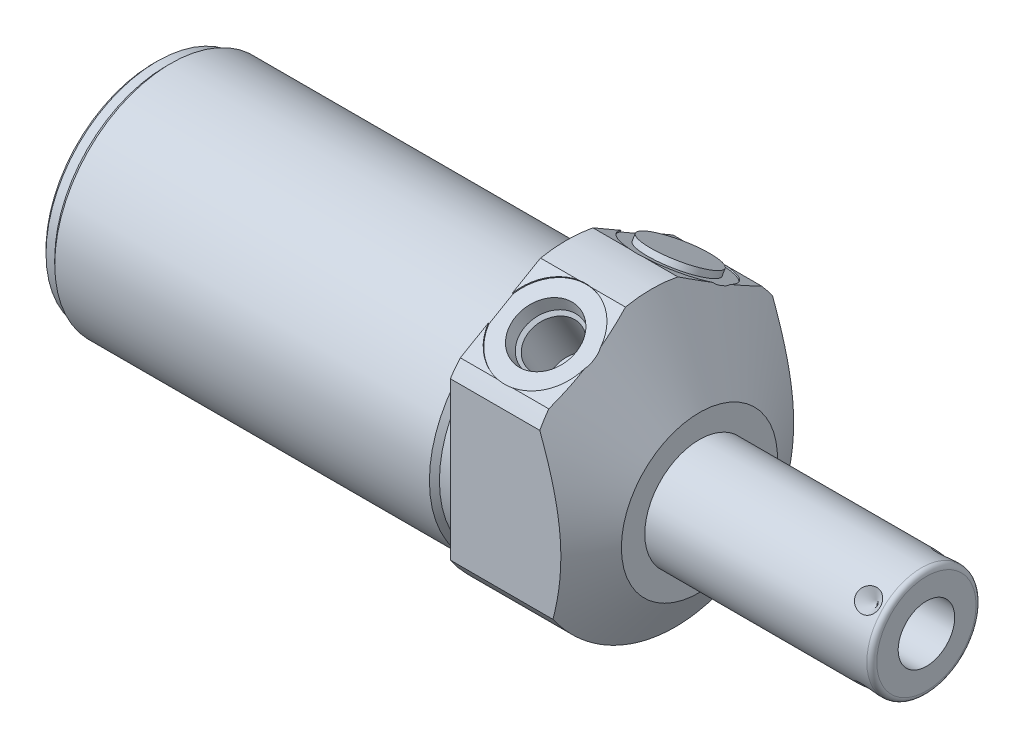
SolidWorks part; units mm, degrees
material "Alloy Steel"
ref_plane "Front Plane" through (0, 0, 0) normal (0, 0, 1) x (1, 0, 0)
ref_plane "Top Plane" through (0, 0, 0) normal (0, 1, 0) x (1, 0, 0)
ref_plane "Right Plane" through (0, 0, 0) normal (1, 0, 0) x (0, 0, -1)
ref_plane "Plane1" through (0, 0, 0) normal (1, 0, 0) x (0, 0, -1)
sketch "Sketch1" plane through (0, 0, 0) normal (1, 0, 0) x (0, 0, -1)
  circle A0 centre (0, 0) radius 28.575
  dimension "D1" = 57.15
extrude "Extrude1" add sketch "Sketch1" along normal blind 27.0002 and the other way blind 84.1248
ref_plane "Plane2" through (0, 0, 0) normal (1, 0, 0) x (0, 0, -1)
sketch "Sketch2" plane through (0, 0, 0) normal (1, 0, 0) x (0, 0, -1)
  line L0 (-25.9842, -4.191) -> (25.9842, -4.191) construction
  circle A0 centre (0, -4.191) radius 23.622
  circle A2 centre (0, 0) radius 28.575
  circle A3 centre (0, 0) radius 28.575
  dimension "D2" = 47.244
  dimension "D1" = 4.191
  dimension "D3" = 0
extrude "Cut-Extrude1" cut sketch "Sketch2" against normal up to next
ref_plane "Plane4" through (0, 0, 0) normal (-1, 0, 0) x (0, 0, 1)
sketch "Sketch4" plane through (0, 0, 0) normal (-1, 0, 0) x (0, 0, 1)
  line L0 (23.6855, -25.6662) -> (23.6855, 17.4761)
  line L1 (23.6855, 17.4761) -> (0, 31.1509)
  line L2 (-23.6855, -25.6662) -> (-23.6855, 17.4761)
  line L3 (-23.6855, 17.4761) -> (0, 31.1509)
  line L4 (0, -31.5613) -> (0, 34.1372) construction
  arc A2 (23.6855, -25.6662) -> (-23.6855, -25.6662) centre (0, 0) ccw
  dimension "D4" = 69.85
  dimension "D1" = 47.371
  dimension "D2" = 30.607
  dimension "D3" = 120
extrude "Cut-Extrude3" cut sketch "Sketch4" against normal up to next
ref_plane "Plane6" through (0, 0, 0) normal (0, 0, 1) x (1, 0, 0)
sketch "Sketch6" plane through (0, 0, 0) normal (0, 0, 1) x (1, 0, 0)
  line L0 (0.7504, 57.15) -> (27.0002, 11.684)
  line L1 (-0.5621, -4.191) -> (28.3127, -4.191) construction
  line L2 (-84.1248, -4.191) -> (0, -4.191) construction
  line L3 (27.0002, 11.684) -> (27.0002, 57.15)
  line L4 (27.0002, 57.15) -> (0.7504, 57.15)
  line L5 (27.0002, 15.9852) -> (27.0002, -15.9852) construction
  dimension "D1" = 60
  dimension "D2" = 31.75
  dimension "D3" = 122.682
revolve "Cut-Revolve2" cut sketch "Sketch6" angle 360 about L1
ref_plane "Plane7" through (9.0932, 23.1369, 13.3727) normal (1, 0, 0) x (0, 0.5, -0.866)
sketch "S2D0002" plane through (9.0932, 23.1369, 13.3727) normal (1, 0, 0) x (0, 0.5, -0.866)
  line L0 (0, 0) -> (6.1849, 0)
  line L1 (6.1849, 0) -> (5.6423, -2.5527)
  line L2 (5.6423, -2.5527) -> (4.9784, -3.2166)
  line L3 (4.9784, -3.2166) -> (4.9784, -13.462)
  line L4 (4.9784, -13.462) -> (0, -13.462)
  line L5 (0, -13.462) -> (0, 0)
  line L6 (0, -14.1351) -> (0, 0.6731) construction
  dimension "D1" = 13.462
revolve "Cut-Revolve3" cut sketch "S2D0002" angle 360 about L6
ref_plane "Plane8" through (9.0932, 23.1369, -13.3727) normal (1, 0, 0) x (0, -0.5, -0.866)
sketch "Sketch8" plane through (9.0932, 23.1369, -13.3727) normal (1, 0, 0) x (0, -0.5, -0.866)
  line L0 (0, 0) -> (6.1849, 0)
  line L1 (6.1849, 0) -> (5.6423, -2.5527)
  line L2 (5.6423, -2.5527) -> (4.9784, -3.2166)
  line L3 (4.9784, -3.2166) -> (4.9784, -13.462)
  line L4 (4.9784, -13.462) -> (0, -13.462)
  line L5 (0, -13.462) -> (0, 0)
  line L6 (0, -14.1351) -> (0, 0.6731) construction
  dimension "D1" = 13.462
revolve "Cut-Revolve4" cut sketch "Sketch8" angle 360 about L6
ref_plane "Plane10" through (0, 0, 0) normal (0, 0, 1) x (1, 0, 0)
sketch "Sketch18" plane through (0, 23.3632, 13.4887) normal (0, 0.866, 0.5) x (1, 0, 0)
  circle A0 centre (9.0932, -0.0127) radius 9.525
  dimension "D1" = 19.05
extrude "Cut-Extrude4" cut sketch "Sketch18" against normal blind 0.254
sketch "Sketch19" plane through (0, 23.3632, -13.4887) normal (0, 0.866, -0.5) x (1, 0, 0)
  circle A0 centre (9.0932, 0.0127) radius 9.525
  circle A1 centre (9.0932, 0.0127) radius 6.1849 construction
  dimension "D1" = 19.05
extrude "Cut-Extrude5" cut sketch "Sketch19" against normal blind 0.254
sketch "Sketch10" plane through (0, 0, 0) normal (0, 0, 1) x (1, 0, 0)
  line L0 (0, 19.431) -> (0, 18.415)
  line L1 (0, 18.415) -> (-3.302, 18.415)
  line L2 (-3.302, 18.415) -> (-4.318, 19.431)
  line L3 (-4.5339, -4.191) -> (0.2159, -4.191) construction
  line L4 (0, 19.431) -> (-4.318, 19.431)
  line L5 (-84.1248, -4.191) -> (0, -4.191) construction
  line L6 (0, 19.431) -> (-84.1248, 19.431) construction
  line L7 (0, 21.9392) -> (0, 18.6529) construction
  dimension "D1" = 45.212
  dimension "D2" = 45
  dimension "D3" = 3.302
revolve "Cut-Revolve6" cut sketch "Sketch10" angle 360 about L3
ref_plane "Plane12" through (0, 0, 0) normal (0, 0, 1) x (1, 0, 0)
sketch "Sketch12" plane through (0, 0, 0) normal (0, 0, 1) x (1, 0, 0)
  line L0 (-84.1248, 19.431) -> (-84.1248, 18.415)
  line L1 (-84.1248, 18.415) -> (-81.5848, 18.415)
  line L2 (-81.5848, 18.415) -> (-80.5688, 19.431)
  line L3 (-84.3026, -4.191) -> (-80.391, -4.191) construction
  line L4 (-84.1248, 19.431) -> (-80.5688, 19.431)
  line L5 (-84.1248, -4.191) -> (-4.318, -4.191) construction
  line L6 (-4.318, 19.431) -> (-84.1248, 19.431) construction
  line L7 (-84.1248, 19.431) -> (-84.1248, -27.813) construction
  dimension "D1" = 45.212
  dimension "D2" = 45
  dimension "D3" = 2.54
revolve "Cut-Revolve8" cut sketch "Sketch12" angle 360 about L3
chamfer "Chamfer1" distance 0.762 angle 45 1 edges at (-84.1248, -4.191, 22.606)
ref_plane "Plane13" through (0, 0, 0) normal (0, 0, 1) x (0, -1, 0)
sketch "Sketch13" plane through (0, 0, 0) normal (0, 0, 1) x (0, -1, 0)
  line L0 (4.191, 27.0002) -> (4.191, 73.2028)
  line L1 (4.191, 73.2028) -> (14.2875, 73.2028)
  line L2 (15.3035, 72.1868) -> (15.3035, 27.0002)
  line L3 (15.3035, 27.0002) -> (4.191, 27.0002)
  line L4 (4.191, 25.1066) -> (4.191, 66.7652) construction
  line L5 (4.191, -80.5688) -> (4.191, -4.318) construction
  line L6 (20.066, 27.0002) -> (-11.684, 27.0002) construction
  line L7 (-18.415, 0) -> (26.797, 0) construction
  arc A0 (15.3035, 72.1868) -> (14.2875, 73.2028) centre (14.2875, 72.1868) ccw
  dimension "D3" = 1.016
  dimension "D1" = 22.225
  dimension "D2" = 73.2028
revolve "Revolve1" add sketch "Sketch13" angle 360 about L4
ref_plane "Plane14" through (64.8716, -9.9441, 0) normal (0, 0, 1) x (0, -1, 0)
sketch "S2D0001" plane through (64.8716, -9.9441, 0) normal (0, 0, 1) x (0, -1, 0)
  line L0 (0, 8.3312) -> (0, -8.6868)
  line L1 (0, -8.6868) -> (-5.7531, -12.1436)
  line L2 (0, 8.3312) -> (-5.7531, 8.3312)
  line L3 (-5.7531, 8.3312) -> (-5.7531, -12.1436)
  line L4 (-5.7531, -21.4986) -> (-5.7531, 1.0237) construction
  line L5 (-5.7531, 7.3152) -> (-5.7531, -37.8714) construction
  line L6 (4.3434, 8.3312) -> (-15.8496, 8.3312) construction
  dimension "D1" = 11.5062
  dimension "D2" = 59
  dimension "D3" = 17.018
revolve "Cut-Revolve9" cut sketch "S2D0001" angle 360 about L4
ref_plane "Plane15" through (27.0002, 23.1432, -13.3617) normal (0, -0.866, 0.5) x (0, -0.5, -0.866)
sketch "Sketch15" plane through (27.0002, 23.1432, -13.3617) normal (0, -0.866, 0.5) x (0, -0.5, -0.866)
  circle A0 centre (0.0127, -17.907) radius 6.9469
  arc A1 (-2.4139, -8.6963) -> (-9.4205, -16.5878) centre (0.0127, -17.907) ccw construction
  dimension "D1" = 13.8938
extrude "Extrude2" add sketch "Sketch15" against normal blind 1.27
ref_plane "Plane16" through (60.9092, -15.3035, 0) normal (0, 0, 1) x (-1, 0, 0)
ref_plane "Plane17" through (0, -2.0955, -2.0955) normal (0, 0.7071, 0.7071) x (-1, 0, 0)
sketch "Sketch16" plane through (60.9092, 3.6667, -7.8577) normal (0, -0.7071, -0.7071) x (-1, 0, 0)
  line L0 (-8.3312, 0) -> (-5.9182, 0)
  line L1 (-5.9182, 0) -> (-8.3312, -2.413)
  line L2 (-8.3312, 0) -> (-8.3312, -2.413)
  line L3 (-8.3312, -4.4865) -> (-8.3312, 0.1207) construction
  line L4 (-12.2936, -1.016) -> (-12.2936, -21.209) construction
  line L5 (33.909, 0) -> (-11.2776, 0) construction
  dimension "D1" = 45
  dimension "D2" = 3.9624
  dimension "D3" = 4.826
revolve "Cut-Revolve10" cut sketch "Sketch16" angle 360 about L3
pattern_circular "CirPattern1" count 4 over 360 about axis through (25.1066, -4.191, 0) along (-1, 0, 0) of "Cut-Revolve10"
